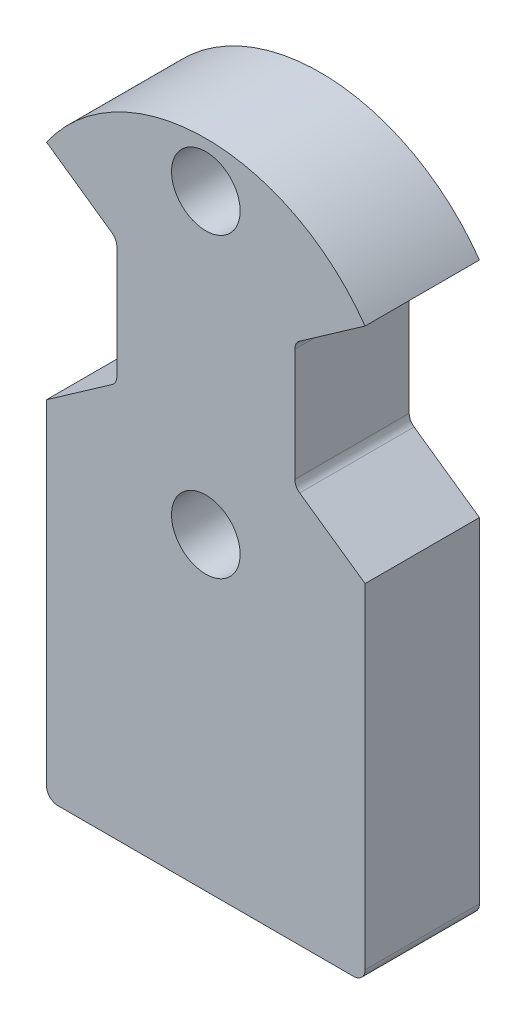
SolidWorks part; units mm, degrees
material "Thornel Mat VMA"
ref_plane "前视基准面" through (0, 0, 0) normal (0, 0, 1) x (1, 0, 0)
ref_plane "上视基准面" through (0, 0, 0) normal (0, 1, 0) x (1, 0, 0)
ref_plane "右视基准面" through (0, 0, 0) normal (1, 0, 0) x (0, 0, -1)
sketch "草图1" plane through (0, 0, 0) normal (0, 0, 1) x (1, 0, 0)
  circle A0 centre (0, 0) radius 8.5
  dimension "D1" = 17
extrude "凸台-拉伸1" add sketch "草图1" along normal blind 5
sketch "草图2" plane through (0, 0, 5) normal (0, 0, 1) x (1, 0, 0)
  circle A0 centre (0, 0) radius 6.5 construction
  circle A1 centre (0, 6.5) radius 1.5
  circle A2 centre (0, -6.5) radius 1.5
  dimension "D1" = 13
  dimension "D2" = 3
extrude "切除-拉伸1" cut sketch "草图2" against normal blind 5
sketch "草图3" plane through (0, 0, 0) normal (0, 0, -1) x (-1, 0, 0)
  line L0 (0, 0) -> (11.6987, 0) construction
  line L1 (0, 0) -> (6.9628, 4.8754)
  line L2 (0, 0) -> (6.9628, -4.8754)
  circle A0 centre (0, 0) radius 4.75
  circle A1 centre (0, 0) radius 8.5
  circle M17 centre (0, 0) radius 8.5
  dimension "D1" = 9.5
  dimension "D2" = 17
  dimension "D3" = 35
  dimension "D4" = 35
extrude "切除-拉伸2" cut sketch "草图3" against normal through all contours A0 L0 A1 L1 | L0 A0 L2 M17
mirror "镜向1" about plane through (0, 0, 0) normal (1, 0, 0) of "切除-拉伸2"
sketch "草图4" plane through (0, 0, 0) normal (0, 0, -1) x (-1, 0, 0)
  line L2 (-6.9628, 4.8754) -> (-6.9628, -20)
  line L3 (-6.9628, -20) -> (6.9628, -20)
  line L4 (6.9628, 4.8754) -> (6.9628, -20)
  line L5 (-2.7947, 8.0274) -> (6.9628, -20) construction
  line L6 (-6.9628, -20) -> (2.7947, 8.0274) construction
  circle A0 centre (0, 0) radius 8.5
  arc M9 (-6.9628, -4.8754) -> (6.9628, -4.8754) centre (0, 0) ccw
  dimension "D1" = 17
  dimension "D2" = 13.9256
  dimension "D3" = 20
extrude "凸台-拉伸2" add sketch "草图4" against normal blind 5 separate body contours L4 L2 L3 M9 | A0
combine bodies "组合1" operation type add bodies to combine 109 110 110
fillet "圆角2" radius 0.5 2 edges at (6.9628, -20, 2.5) (-6.9628, -20, 2.5)
sketch "草图6" plane through (0, 0, 0) normal (0, 0, -1) x (-1, 0, 0)
  line L1 (-3.891, 2.7245) -> (3.891, 2.7245)
  line L2 (-3.891, 2.7245) -> (-3.891, -2.7245)
  line L3 (-3.891, -2.7245) -> (3.891, -2.7245)
  line L4 (3.891, 2.7245) -> (3.891, -2.7245)
  circle A0 centre (0, 0) radius 4.75
  arc A1 (3.891, -2.7245) -> (3.891, 2.7245) centre (0, 0) ccw construction
  arc M9 (3.891, -2.7245) -> (3.891, 2.7245) centre (0, 0) ccw
  arc M13 (-3.891, 2.7245) -> (-3.891, -2.7245) centre (0, 0) ccw
extrude "切除-拉伸3" cut sketch "草图6" against normal blind 10 contours L4 M9 | L2 M13
fillet "圆角3" radius 0.5 4 edges at (3.891, 2.7245, 2.5) (3.891, -2.7245, 2.5) (-3.891, -2.7245, 2.5) (-3.891, 2.7245, 2.5)
